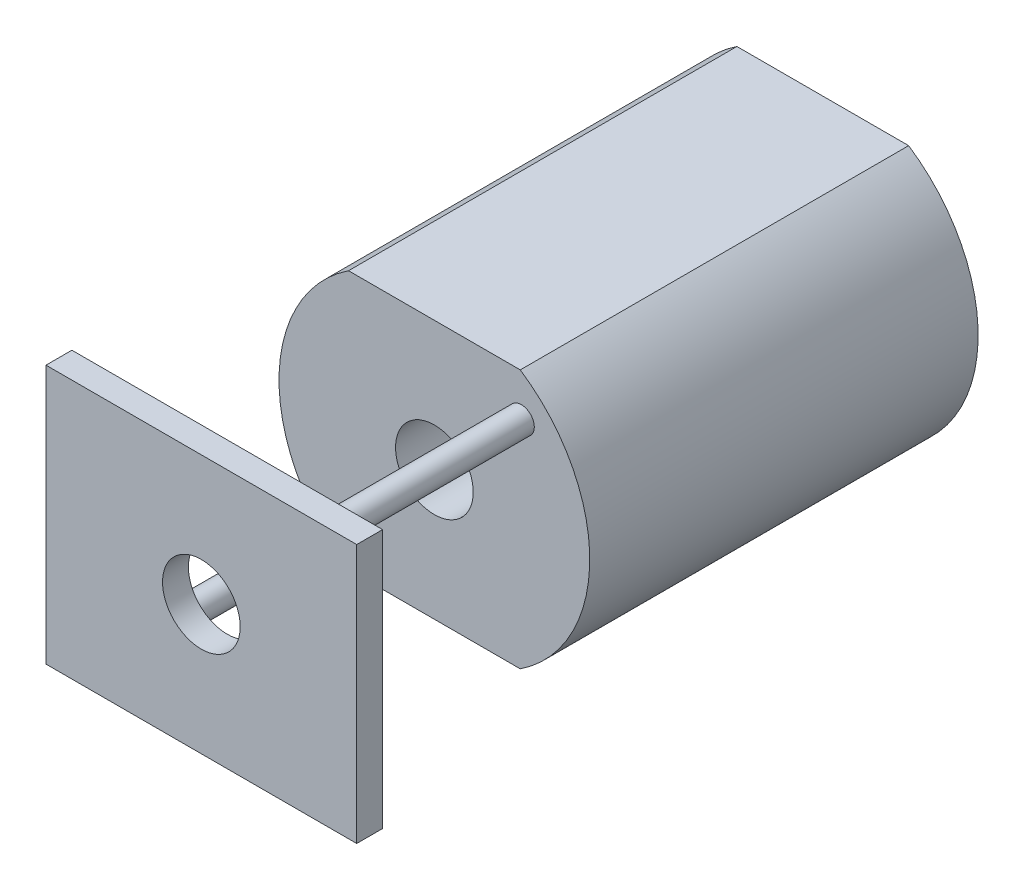
SolidWorks part; units mm, degrees
ref_plane "Front Plane" through (0, 0, 0) normal (0, 0, 1) x (1, 0, 0)
ref_plane "Top Plane" through (0, 0, 0) normal (0, 1, 0) x (1, 0, 0)
ref_plane "Right Plane" through (0, 0, 0) normal (1, 0, 0) x (0, 0, -1)
sketch "Sketch1" plane through (0, 0, 0) normal (0, 0, 1) x (1, 0, 0)
  line L0 (0, 0) -> (3919.9789, 0) construction
  line L1 (0, 0) -> (0, -3919.9789) construction
  line L2 (-3.3166, 5) -> (3.3166, 5)
  line L3 (-3.3166, -5) -> (3.3166, -5)
  arc A0 (-3.3166, 5) -> (-3.3166, -5) centre (0, 0) ccw
  arc A1 (3.3166, -5) -> (3.3166, 5) centre (0, 0) ccw
  point P6 (0, 0)
  dimension "D1" = 12
  dimension "D2" = 10
extrude "Boss-Extrude1" add sketch "Sketch1" along normal mid plane 15
sketch "Sketch2" plane through (0, 0, -7.5) normal (0, 0, -1) x (-1, 0, 0)
  circle A0 centre (0, 0) radius 2.5
  dimension "D1" = 5
extrude "Boss-Extrude2" add sketch "Sketch2" along normal blind 1
sketch "Sketch3" plane through (0, 0, 7.5) normal (0, 0, 1) x (1, 0, 0)
  line L0 (5.3611, 5.3611) -> (-5.3611, -5.3611) construction
  line L1 (0, 0) -> (1.4666, 0) construction
  circle A0 centre (3.3588, 3.3588) radius 0.5
  circle A1 centre (-3.3588, -3.3588) radius 0.5
  point P4 (0, 0)
  point P10 (0, 0)
  point P11 (0, 0)
  point P12 (3.3932, 3.3932)
  dimension "D2" = 1
  dimension "D3" = 1
  dimension "D1" = 45
  dimension "D4" = 4.75
  dimension "D5" = 4.75
extrude "Boss-Extrude3" add sketch "Sketch3" along normal blind 9
sketch "Sketch4" plane through (0, 0, 16.5) normal (0, 0, 1) x (1, 0, 0)
  line L1 (-6, -5) -> (6, -5)
  line L2 (-6, -5) -> (-6, 5)
  line L3 (-6, 5) -> (6, 5)
  line L4 (6, -5) -> (6, 5)
  line L5 (-6, -5) -> (6, 5) construction
  line L6 (-6, 5) -> (6, -5) construction
  point P0 (0, 0)
  dimension "D1" = 12
  dimension "D2" = 10
extrude "Boss-Extrude4" add sketch "Sketch4" against normal blind 1
sketch "Sketch5" plane through (0, 0, 16.5) normal (0, 0, 1) x (1, 0, 0)
  circle A0 centre (0, 0) radius 1.5
  circle A1 centre (0, 0) radius 1.7
  dimension "D1" = 3
  dimension "D2" = 0.2
extrude "Cut-Extrude1" cut sketch "Sketch5" against normal through all contours A0
